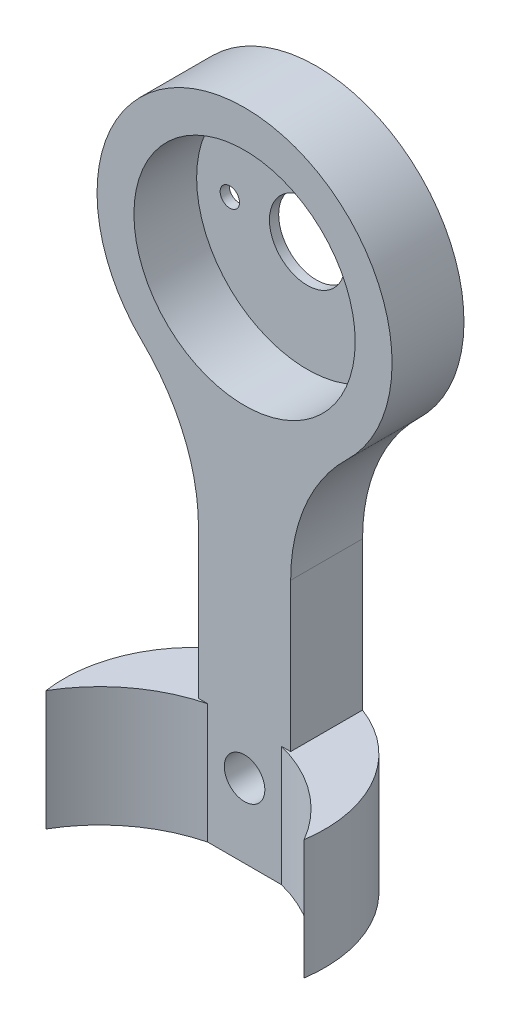
SolidWorks part; units mm, degrees
material "Nylon 101"
ref_plane "Front Plane" through (0, 0, 0) normal (0, 0, 1) x (1, 0, 0)
ref_plane "Top Plane" through (0, 0, 0) normal (0, 1, 0) x (1, 0, 0)
ref_plane "Right Plane" through (0, 0, 0) normal (1, 0, 0) x (0, 0, -1)
sketch "Sketch1" plane through (0, 0, 0) normal (0, 0, 1) x (1, 0, 0)
  line L0 (-2.5, -27.5) -> (2.5, -27.5)
  line L2 (-2.5, -12.9518) -> (-2.5, -27.5)
  line L4 (2.5, -12.9518) -> (2.5, -27.5)
  circle A0 centre (0, 0) radius 6
  arc A1 (5.5556, -5.7564) -> (-5.5556, -5.7564) centre (0, 0) ccw
  arc A2 (5.5556, -5.7564) -> (2.5, -12.9518) centre (12.5, -12.9518) ccw
  arc A3 (-5.5556, -5.7564) -> (-2.5, -12.9518) centre (-12.5, -12.9518) cw
  circle A4 centre (0, -23.5) radius 1.1
  point P5 (0, -27.5)
  dimension "D1" = 12
  dimension "D2" = 2
  dimension "D5" = 10
  dimension "D4" = 2.2
  dimension "D3" = 23.5
  dimension "D6" = 4
  dimension "D7" = 5
extrude "Boss-Extrude1" add sketch "Sketch1" along normal blind 3.9
sketch "Sketch4" plane through (0, 0, 0) normal (0, 0, 1) x (1, 0, 0)
  line L0 (4.2, 0) -> (-4.2, 0) construction
  circle A0 centre (0, 0) radius 8
  circle A1 centre (0, 0) radius 6
  circle A2 centre (0, 0) radius 6 construction
  arc A3 (5.5556, -5.7564) -> (-5.5556, -5.7564) centre (0, 0) ccw construction
  circle A4 centre (4.2, 0) radius 0.525
  circle A5 centre (-4.2, 0) radius 0.525
  point P16 (0, 0)
  dimension "D1" = 1.05
  dimension "D2" = 8.4
sketch "Sketch5" plane through (0, 0, 0) normal (0, 0, -1) x (-1, 0, 0)
  circle A0 centre (0, 0) radius 2.05
  circle A1 centre (4.2, 0) radius 0.525
  circle A2 centre (4.2, 0) radius 0.525
  circle A3 centre (-4.2, 0) radius 0.525
  circle A4 centre (-4.2, 0) radius 0.525
  circle A7 centre (0, 0) radius 8
  circle A8 centre (0, 0) radius 8
  dimension "D3" = 4.1
  dimension "D1" = 0
  dimension "D2" = 0
  dimension "D4" = 0
extrude "Boss-Extrude3" add sketch "Sketch5" against normal blind 0.5
sketch "Sketch7" plane through (0, -27.5, 0) normal (0, -1, 0) x (1, 0, 0)
  line L2 (-2.5, 0) -> (2.5, 0) construction
  line L3 (1.9978, 3.9) -> (2.5, 0)
  line L4 (0, 0) -> (0, 10.3958) construction
  line L5 (-1.9978, 3.9) -> (-2.5, 0)
  arc A0 (-7, 7.6669) -> (-1.9978, 3.9) centre (0, 11.7577) ccw construction
  arc A1 (1.9978, 3.9) -> (7, 7.6669) centre (0, 11.7577) ccw construction
  arc A2 (-7, 7.6669) -> (-1.9978, 3.9) centre (0, 11.7577) ccw
  arc A3 (1.9978, 3.9) -> (7, 7.6669) centre (0, 11.7577) ccw
  arc A4 (7, 7.6669) -> (2.5, 0) centre (0, 6.6214) cw
  arc A5 (-1.9978, 3.9) -> (-7, 7.6669) centre (0, 11.7577) cw
  arc A6 (-7, 7.6669) -> (-2.5, 0) centre (0, 6.6214) ccw
  point P11 (0, 0)
  line M6 (2.5, 0) -> (2.5, 3.9)
  line M7 (2.5, 3.9) -> (-2.5, 3.9)
  line M8 (-2.5, 3.9) -> (-2.5, 0)
extrude "Boss-Extrude4" add sketch "Sketch7" against normal up to surface (6.5 mm away) contours A4 A3 M7 M6 | A2 A6 M8 M7
